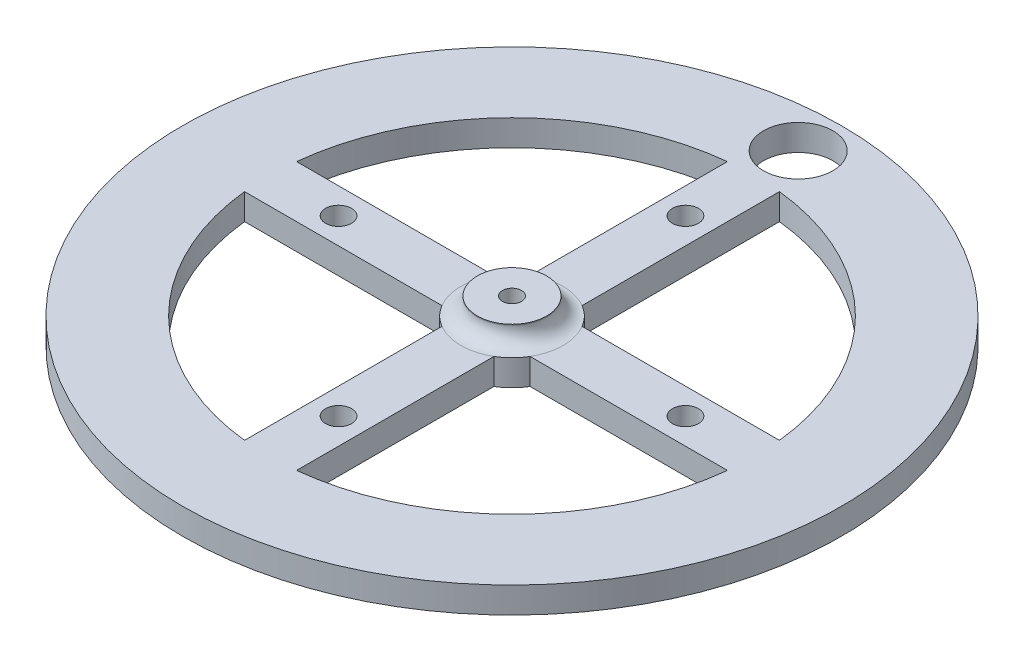
SolidWorks part; units mm, degrees
ref_plane "Plano frontal" through (0, 0, 0) normal (0, 0, 1) x (1, 0, 0)
ref_plane "Plano superior" through (0, 0, 0) normal (0, 1, 0) x (1, 0, 0)
ref_plane "Plano direito" through (0, 0, 0) normal (1, 0, 0) x (0, 0, -1)
sketch "Esboço1" plane through (0, 0, 0) normal (0, 0, 1) x (1, 0, 0)
  line L0 (0, 0) -> (0, 5.1163) construction
  line L1 (1.1, 5) -> (1.1, 0)
  line L2 (1.1, 0) -> (38, 0)
  line L3 (38, 0) -> (38, 3)
  line L4 (38, 3) -> (5.9, 3)
  line L5 (4, 4.9) -> (4, 5)
  line L6 (4, 5) -> (1.1, 5)
  arc A0 (5.9, 3) -> (4, 4.9) centre (5.9, 4.9) cw
  point P10 (8.9767, 0)
  point P12 (5.1395, 3)
  point P13 (5.7442, 3)
  point P14 (10.6434, 3)
  point P15 (2.5, 12.3309)
  dimension "D1" = 2.2
  dimension "D2" = 8
  dimension "D3" = 3
  dimension "D4" = 5
  dimension "D5" = 76
  dimension "D6" = 0.1
revolve "Revolução1" add sketch "Esboço1" angle 360 about L0
sketch "Esboço2" plane through (0, 0, 0) normal (0, 1, 0) x (1, 0, 0)
  circle A0 centre (0, 20) radius 3
  circle A1 centre (0, 20) radius 1.5
  point P3 (0, 11.8863)
  dimension "D2" = 3
  dimension "D3" = 6
  dimension "D1" = 20
extrude "Corte-extrusão4" cut sketch "Esboço2" against normal through all and the other way through all contours A1
sketch "Esboço6" plane through (0, 3, 0) normal (0, 1, 0) x (1, 0, 0)
  line L0 (0, 38) -> (0, 0) construction
  line L1 (0, 0) -> (25.7, 0) construction
  line L2 (3, 27.8388) -> (3, 5.0804)
  line L3 (28, 0) -> (33, 0) construction
  line L4 (33, 0) -> (38, 0) construction
  line L5 (27.8388, 3) -> (5.0804, 3)
  circle A0 centre (0, 0) radius 38 construction
  arc A1 (5.0804, 3) -> (3, 5.0804) centre (0, 0) ccw
  arc A2 (27.8388, 3) -> (3, 27.8388) centre (0, 0) ccw
  circle A3 centre (0, 0) radius 33 construction
  circle A4 centre (0, 0) radius 38 construction
  circle A5 centre (0, 0) radius 5.9 construction
  point P10 (0, 0)
  point P12 (5.7663, 3)
  dimension "D4" = 66
  dimension "D1" = 6
  dimension "D3" = 6
extrude "Corte-extrusão9" cut sketch "Esboço6" against normal through all both and the other way through all
pattern_circular "PadrãoCircular1" count 4 over 360 about axis through (0, 0, 0) along (0, 1, 0) of "Corte-extrusão4", "Corte-extrusão9"
sketch "Esboço7" plane through (0, 3, 0) normal (0, 1, 0) x (1, 0, 0)
  line L0 (0, 38) -> (0, 0) construction
  circle A0 centre (0, 33) radius 4
  circle A1 centre (0, 0) radius 33 construction
  point P2 (5.3596, 32.5619)
  point P5 (0, 33)
  dimension "D1" = 8
extrude "Corte-extrusão10" cut sketch "Esboço7" against normal blind 10
equation "\"D3@Esboço6\"=\"D1@Esboço6\""
